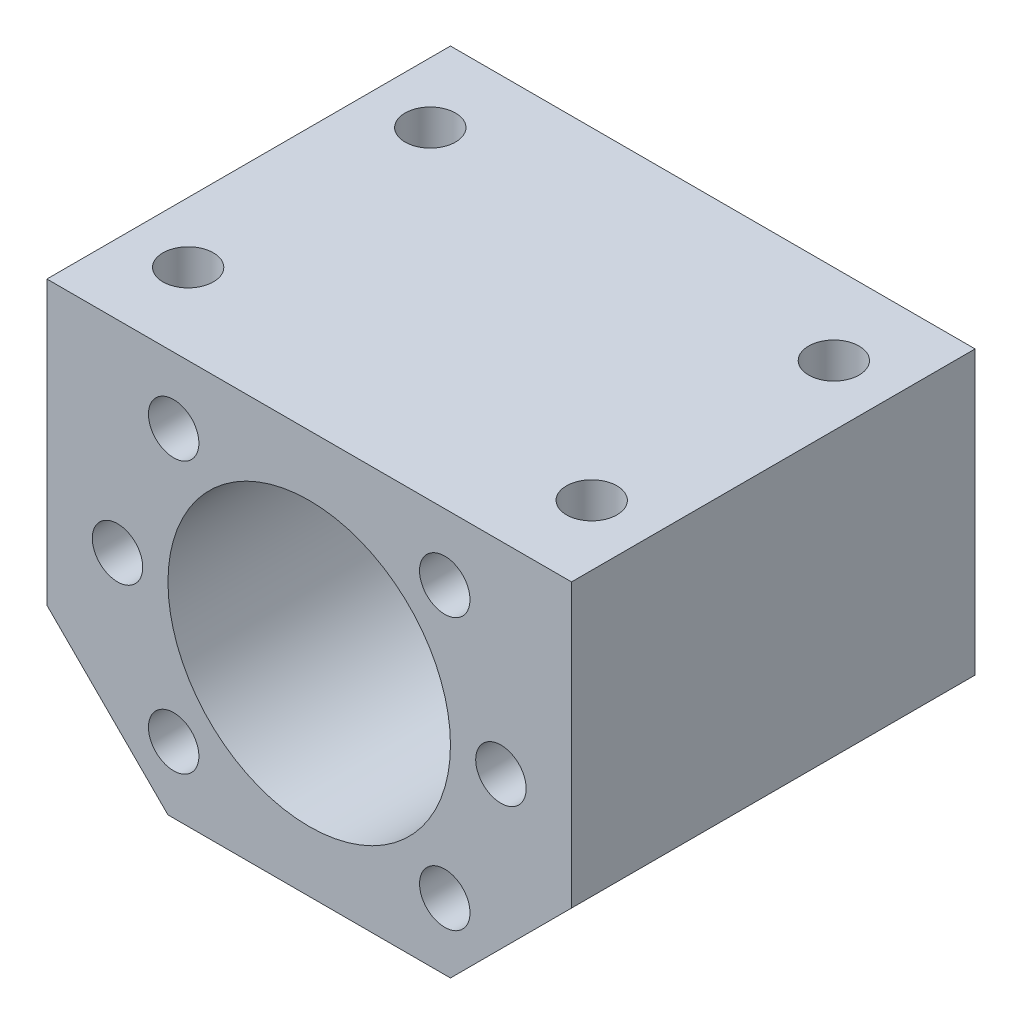
SolidWorks part; units mm, degrees
material "6061 合金"
ref_plane "前视基准面" through (0, 0, 0) normal (0, 0, 1) x (1, 0, 0)
ref_plane "上视基准面" through (0, 0, 0) normal (0, 1, 0) x (1, 0, 0)
ref_plane "右视基准面" through (0, 0, 0) normal (1, 0, 0) x (0, 0, -1)
sketch "草图1" plane through (0, 0, 0) normal (0, 0, 1) x (1, 0, 0)
  line L0 (0, 24.6031) -> (0, -23.325) construction
  line L1 (-29.6355, 0) -> (26.1208, 0) construction
  line L2 (26, 20) -> (-26, 20)
  line L3 (-26, 20) -> (-26, -8)
  line L4 (-26, -8) -> (-14, -20)
  line L5 (-14, -20) -> (14, -20)
  line L6 (26, -8) -> (14, -20)
  line L7 (26, 20) -> (26, -8)
  circle A0 centre (0, 0) radius 14
  circle A1 centre (0, 0) radius 19 construction
  circle A2 centre (-19, 0) radius 2.5
  circle A3 centre (-13.435, 13.435) radius 2.5
  circle A4 centre (-13.435, -13.435) radius 2.5
  circle A5 centre (13.435, -13.435) radius 2.5
  circle A6 centre (13.435, 13.435) radius 2.5
  circle A7 centre (19, 0) radius 2.5
  point P14 (0, -20)
  point P16 (0, 20)
  dimension "D1" = 28
  dimension "D7" = 38
  dimension "D8" = 5
  dimension "D2" = 40
  dimension "D3" = 20
  dimension "D4" = 52
  dimension "D5" = 12
  dimension "D6" = 12
  dimension "D9" = 90
extrude "凸台-拉伸1" add sketch "草图1" along normal blind 40
sketch "草图3" plane through (0, 20, 0) normal (0, 1, 0) x (1, 0, 0)
  line L0 (0, 0) -> (0, -40) construction
  line L1 (26, 0) -> (-26, 0) construction
  line L2 (26, -40) -> (-26, -40) construction
  circle A0 centre (-20, -8) radius 2.5
  circle A1 centre (-20, -32) radius 2.5
  circle A2 centre (20, -32) radius 2.5
  circle A3 centre (20, -8) radius 2.5
  dimension "D1" = 5
  dimension "D2" = 8
  dimension "D3" = 24
  dimension "D4" = 40
extrude "切除-拉伸1" cut sketch "草图3" against normal blind 10
